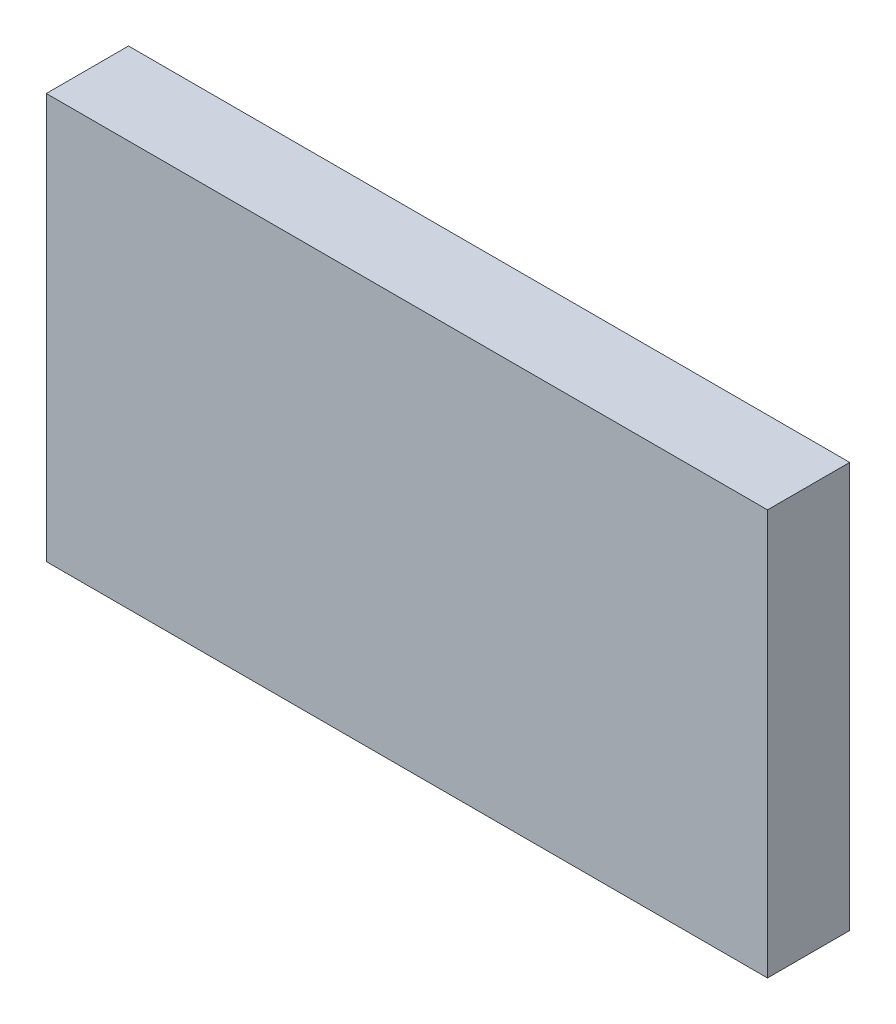
SolidWorks part; units mm, degrees
ref_plane "Front Plane" through (0, 0, 0) normal (0, 0, 1) x (1, 0, 0)
ref_plane "Top Plane" through (0, 0, 0) normal (0, 1, 0) x (1, 0, 0)
ref_plane "Right Plane" through (0, 0, 0) normal (1, 0, 0) x (0, 0, -1)
sketch "Sketch2" plane through (0, 0, 0) normal (0, 0, 1) x (1, 0, 0)
  line L1 (0, 0) -> (87.7223, 0)
  line L2 (0, 0) -> (0, 49.3121)
  line L3 (0, 49.3121) -> (87.7223, 49.3121)
  line L4 (87.7223, 0) -> (87.7223, 49.3121)
extrude "Extrude1" add sketch "Sketch2" along normal blind 10
